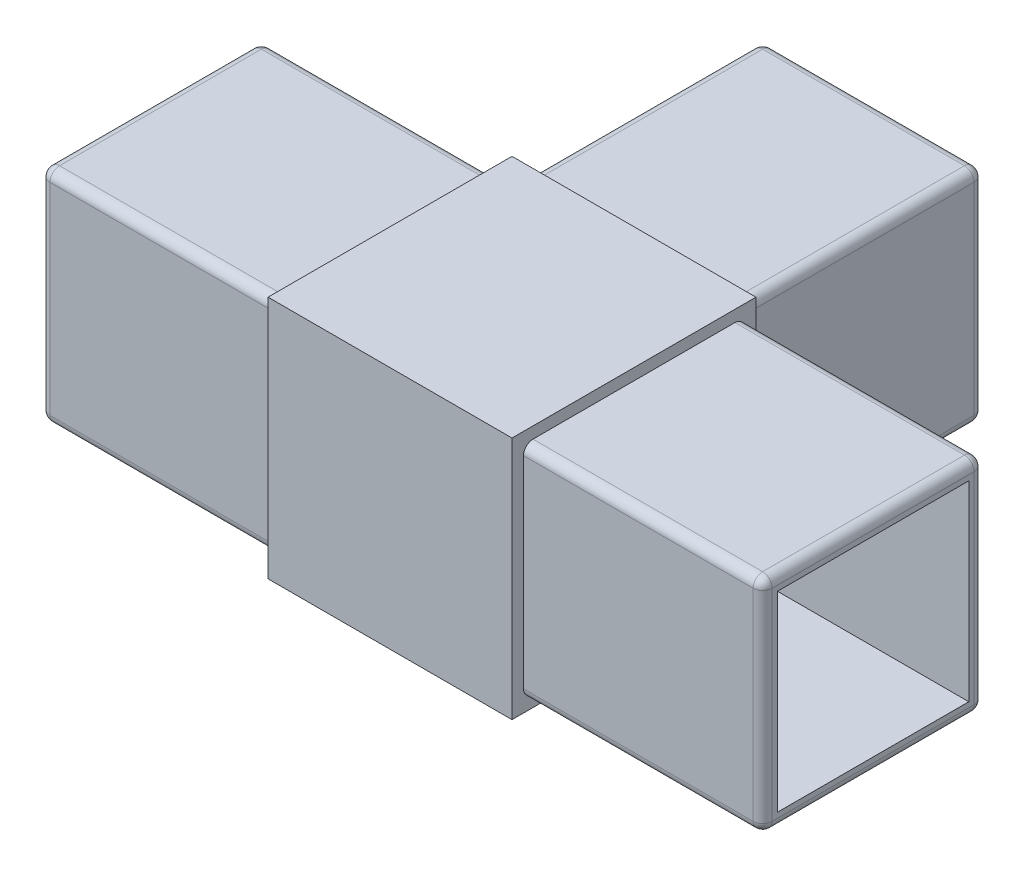
SolidWorks part; units mm, degrees
material "PBT General Purpose"
ref_plane "Front" through (0, 0, 0) normal (0, 0, 1) x (1, 0, 0)
ref_plane "Top" through (0, 0, 0) normal (0, 1, 0) x (1, 0, 0)
ref_plane "Right" through (0, 0, 0) normal (1, 0, 0) x (0, 0, -1)
sketch "Sketch1" plane through (0, 0, 0) normal (0, 1, 0) x (1, 0, 0)
  line L0 (-11.55, 12.75) -> (11.55, 12.75)
  line L1 (-12.75, 12.75) -> (12.75, 12.75)
  line L2 (-12.75, 12.75) -> (-12.75, -12.75)
  line L3 (-12.75, -12.75) -> (12.75, -12.75)
  line L4 (12.75, 12.75) -> (12.75, -12.75)
  line L5 (-12.75, 12.75) -> (12.75, -12.75) construction
  line L6 (-12.75, -12.75) -> (12.75, 12.75) construction
  line L8 (-37.75, 11.55) -> (-37.75, -11.55)
  line L10 (37.75, 11.55) -> (37.75, -11.55)
  line L11 (37.75, 11.55) -> (12.75, 11.55)
  line L12 (12.75, 11.55) -> (12.75, -11.55)
  line L15 (11.55, 37.75) -> (-11.55, 37.75)
  line L17 (12.75, -11.55) -> (37.75, -11.55)
  line L18 (-37.75, -11.55) -> (-12.75, -11.55)
  line L22 (11.55, 12.75) -> (11.55, 37.75)
  line L23 (-11.55, 12.75) -> (-11.55, 37.75)
  line L24 (-12.75, -11.55) -> (-12.75, 11.55)
  line L25 (-12.75, 11.55) -> (-37.75, 11.55)
  line L26 (37.75, 0) -> (-37.75, 0) construction
  line L27 (0, 0) -> (0, 37.75) construction
  point P0 (0, 0)
  point P6 (0, 0)
  point P11 (0, 0)
  point P19 (0, 0)
  point P26 (0, 0)
  point P27 (0, 0)
  dimension "D1" = 25
  dimension "D2" = 25.5
  dimension "D3" = 23.1
extrude "Boss-Extrude2" add sketch "Sketch1" along normal blind 25.5 contours L2 L25 L8 L18 | L4 L1 L0 L2 L3 | L23 L0 L22 L15 | L4 L17 L10 L11
sketch "Sketch2" plane through (37.75, 0, 0) normal (1, 0, 0) x (0, 0, -1)
  line L0 (11.55, 25.5) -> (11.55, 0) construction
  line L1 (-11.55, 25.5) -> (11.55, 25.5)
  line L2 (-11.55, 25.5) -> (-11.55, 24.3)
  line L3 (-11.55, 24.3) -> (11.55, 24.3)
  line L4 (11.55, 25.5) -> (11.55, 24.3)
  line L5 (-11.55, 25.5) -> (-11.55, 0) construction
  line L6 (11.55, 0) -> (-11.55, 0)
  line L7 (11.55, 0) -> (11.55, 1.2)
  line L8 (11.55, 1.2) -> (-11.55, 1.2)
  line L9 (-11.55, 0) -> (-11.55, 1.2)
  dimension "D1" = 1.2
extrude "Cut-Extrude1" cut sketch "Sketch2" against normal blind 25
sketch "Sketch3" plane through (-37.75, 0, 0) normal (-1, 0, 0) x (0, 0, 1)
  line L0 (11.55, 25.5) -> (11.55, 0) construction
  line L1 (-11.55, 25.5) -> (11.55, 25.5)
  line L2 (-11.55, 25.5) -> (-11.55, 24.3)
  line L3 (-11.55, 24.3) -> (11.55, 24.3)
  line L4 (11.55, 25.5) -> (11.55, 24.3)
  line L5 (-11.55, 25.5) -> (-11.55, 0) construction
  line L6 (11.55, 0) -> (-11.55, 0)
  line L7 (11.55, 0) -> (11.55, 1.2)
  line L8 (11.55, 1.2) -> (-11.55, 1.2)
  line L9 (-11.55, 0) -> (-11.55, 1.2)
  dimension "D1" = 1.2
extrude "Cut-Extrude2" cut sketch "Sketch3" against normal blind 25
sketch "Sketch4" plane through (0, 0, -37.75) normal (0, 0, -1) x (-1, 0, 0)
  line L0 (11.55, 25.5) -> (11.55, 0) construction
  line L1 (-11.55, 25.5) -> (11.55, 25.5)
  line L2 (-11.55, 25.5) -> (-11.55, 24.3)
  line L3 (-11.55, 24.3) -> (11.55, 24.3)
  line L4 (11.55, 25.5) -> (11.55, 24.3)
  line L5 (-11.55, 25.5) -> (-11.55, 0) construction
  line L6 (11.55, 0) -> (-11.55, 0)
  line L7 (11.55, 0) -> (11.55, 1.2)
  line L8 (11.55, 1.2) -> (-11.55, 1.2)
  line L9 (-11.55, 0) -> (-11.55, 1.2)
  dimension "D1" = 1.2
extrude "Cut-Extrude3" cut sketch "Sketch4" against normal blind 25
sketch "Sketch5" plane through (37.75, 0, 0) normal (1, 0, 0) x (0, 0, -1)
  line L0 (-11.55, 24.3) -> (11.55, 1.2) construction
  line L2 (-10, 22.75) -> (10, 22.75)
  line L3 (-10, 22.75) -> (-10, 2.75)
  line L4 (-10, 2.75) -> (10, 2.75)
  line L5 (10, 22.75) -> (10, 2.75)
  line L6 (-10, 22.75) -> (10, 2.75) construction
  line L7 (-10, 2.75) -> (10, 22.75) construction
  point P4 (0, 12.75)
  dimension "D1" = 20
extrude "Cut-Extrude4" cut sketch "Sketch5" against normal through all
sketch "Sketch8" plane through (0, 0, -37.75) normal (0, 0, -1) x (-1, 0, 0)
  line L0 (-11.55, 24.3) -> (11.55, 1.2) construction
  line L2 (-10, 22.75) -> (10, 22.75)
  line L3 (-10, 22.75) -> (-10, 2.75)
  line L4 (-10, 2.75) -> (10, 2.75)
  line L5 (10, 22.75) -> (10, 2.75)
  line L6 (-10, 22.75) -> (10, 2.75) construction
  line L7 (-10, 2.75) -> (10, 22.75) construction
  point P4 (0, 12.75)
  dimension "D1" = 20
extrude "Cut-Extrude5" cut sketch "Sketch8" against normal blind 30
fillet "Fillet1" radius 1 24 edges at (37.75, 1.2, 0) (37.75, 12.75, 11.55) (37.75, 24.3, 0) (37.75, 12.75, -11.55) (25.25, 1.2, 11.55) (25.25, 1.2, -11.55) (25.25, 24.3, 11.55) (25.25, 24.3, -11.55) (0, 1.2, -37.75) (11.55, 12.75, -37.75) (0, 24.3, -37.75) (-11.55, 12.75, -37.75) (11.55, 1.2, -25.25) (-11.55, 1.2, -25.25) (11.55, 24.3, -25.25) (-11.55, 24.3, -25.25) (-37.75, 1.2, 0) (-37.75, 24.3, 0) (-37.75, 12.75, 11.55) (-37.75, 12.75, -11.55) (-25.25, 1.2, -11.55) (-25.25, 1.2, 11.55) (-25.25, 24.3, 11.55) (-25.25, 24.3, -11.55)
